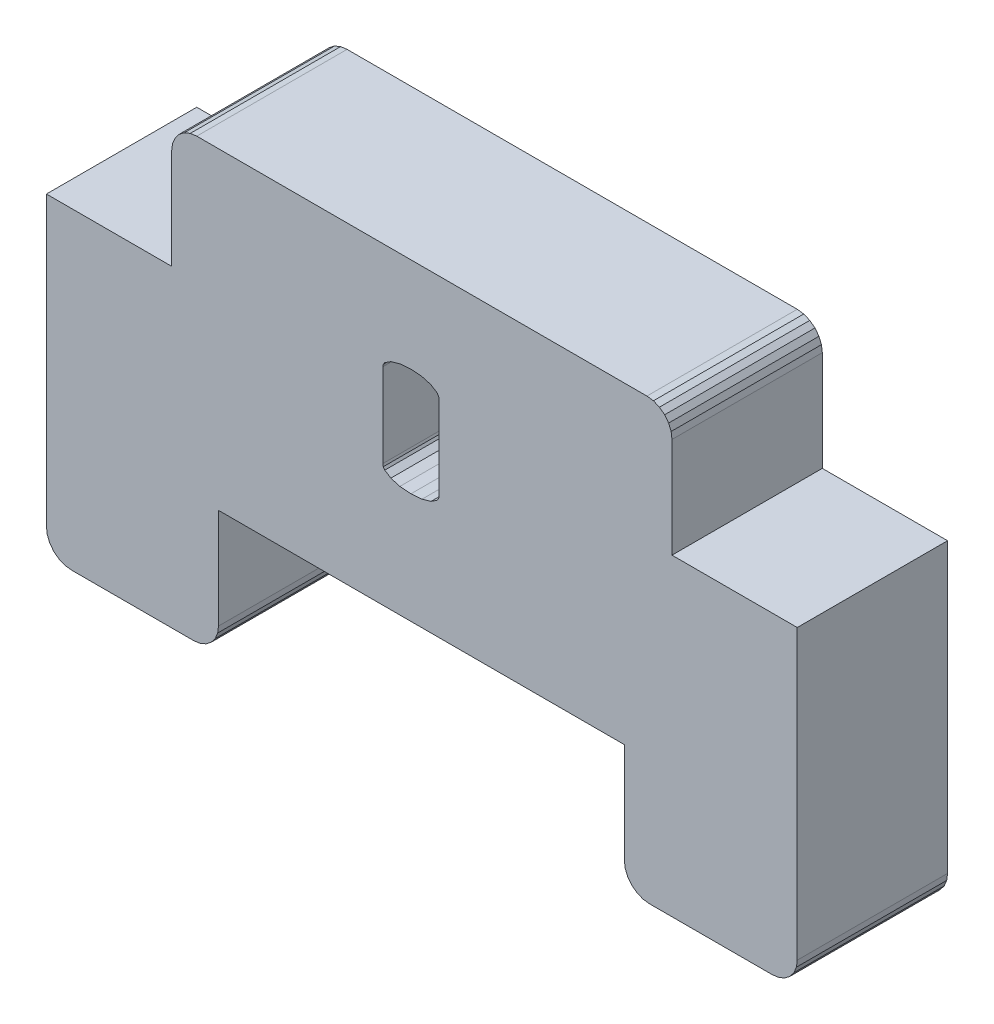
SolidWorks part; units mm, degrees
material "Maple"
ref_plane "Front Plane" through (0, 0, 0) normal (0, 0, 1) x (1, 0, 0)
ref_plane "Top Plane" through (0, 0, 0) normal (0, 1, 0) x (1, 0, 0)
ref_plane "Right Plane" through (0, 0, 0) normal (1, 0, 0) x (0, 0, -1)
sketch "Sketch1" plane through (0, 0, 0) normal (0, 0, 1) x (1, 0, 0)
  line L319 (-339.6271, -185.5951) -> (-339.5272, -185.8363)
  line L320 (-339.6612, -185.3363) -> (-339.6271, -185.5951)
  line L321 (-332.7612, -185.3363) -> (-332.7612, -173.8363)
  line L322 (-333.0541, -186.0434) -> (-333.2612, -186.2023)
  line L323 (-338.2612, -168.9703) -> (-338.5024, -168.8704)
  line L324 (-338.0541, -169.1292) -> (-338.2612, -168.9703)
  line L325 (-337.8952, -169.3363) -> (-338.0541, -169.1292)
  line L326 (-338.6612, -186.3363) -> (-333.7612, -186.3363)
  line L327 (-339.6612, -181.3363) -> (-339.6612, -185.3363)
  line L328 (-355.8612, -181.3363) -> (-339.6612, -181.3363)
  line L329 (-357.7297, -173.8363) -> (-357.7297, -169.8363)
  line L330 (-362.4368, -186.0434) -> (-362.5957, -185.8363)
  line L331 (-362.2297, -186.2023) -> (-362.4368, -186.0434)
  line L332 (-361.9885, -186.3022) -> (-362.2297, -186.2023)
  line L333 (-361.7297, -186.3363) -> (-356.8612, -186.3363)
  line L334 (-337.7612, -173.8363) -> (-332.7612, -173.8363)
  line L335 (-357.4368, -169.1292) -> (-357.2297, -168.9703)
  line L336 (-338.92, -186.3022) -> (-338.6612, -186.3363)
  line L337 (-361.7297, -186.3363) -> (-361.9885, -186.3022)
  line L338 (-356.6024, -186.3022) -> (-356.8612, -186.3363)
  line L339 (-356.9885, -168.8704) -> (-356.7297, -168.8363)
  line L340 (-356.7297, -168.8363) -> (-338.7612, -168.8363)
  line L341 (-333.2612, -186.2023) -> (-333.5024, -186.3022)
  line L342 (-362.7297, -173.8363) -> (-362.7297, -185.3363)
  line L343 (-357.7297, -173.8363) -> (-362.7297, -173.8363)
  line L344 (-357.2297, -168.9703) -> (-356.9885, -168.8704)
  line L345 (-357.5957, -169.3363) -> (-357.4368, -169.1292)
  line L346 (-357.6956, -169.5775) -> (-357.5957, -169.3363)
  line L347 (-357.7297, -169.8363) -> (-357.6956, -169.5775)
  line L348 (-362.6956, -185.5951) -> (-362.7297, -185.3363)
  line L349 (-362.5957, -185.8363) -> (-362.6956, -185.5951)
  line L350 (-356.3612, -186.2023) -> (-356.6024, -186.3022)
  line L351 (-356.1541, -186.0434) -> (-356.3612, -186.2023)
  line L352 (-355.9952, -185.8363) -> (-356.1541, -186.0434)
  line L353 (-355.8953, -185.5951) -> (-355.9952, -185.8363)
  line L354 (-355.8612, -185.3363) -> (-355.8953, -185.5951)
  line L355 (-355.8612, -185.3363) -> (-355.8612, -181.3363)
  line L356 (-339.5272, -185.8363) -> (-339.3683, -186.0434)
  line L357 (-339.3683, -186.0434) -> (-339.1612, -186.2023)
  line L358 (-339.1612, -186.2023) -> (-338.92, -186.3022)
  line L359 (-333.5024, -186.3022) -> (-333.7612, -186.3363)
  line L360 (-332.8952, -185.8363) -> (-333.0541, -186.0434)
  line L361 (-332.7953, -185.5951) -> (-332.8952, -185.8363)
  line L362 (-332.7612, -185.3363) -> (-332.7953, -185.5951)
  line L363 (-337.7612, -169.8363) -> (-337.7612, -173.8363)
  line L364 (-337.7612, -169.8363) -> (-337.7953, -169.5775)
  line L365 (-337.7953, -169.5775) -> (-337.8952, -169.3363)
  line L366 (-338.5024, -168.8704) -> (-338.7612, -168.8363)
  line L8572 (-349.3045, -176.444) -> (-349.2844, -176.5403)
  line L8573 (-349.2844, -176.5403) -> (-349.2241, -176.629)
  line L8574 (-349.2241, -176.629) -> (-348.9829, -176.7844)
  line L8575 (-348.9829, -176.7844) -> (-348.6216, -176.8897)
  line L8576 (-348.6216, -176.8897) -> (-348.1806, -176.9249)
  line L8577 (-348.1806, -176.9249) -> (-347.7396, -176.8897)
  line L8578 (-347.7396, -176.8897) -> (-347.3782, -176.7844)
  line L8579 (-347.3782, -176.7844) -> (-347.1371, -176.629)
  line L8580 (-347.1371, -176.629) -> (-347.0768, -176.5403)
  line L8581 (-347.0768, -176.5403) -> (-347.0567, -176.444)
  line L8582 (-347.0567, -176.444) -> (-347.0567, -173.0973)
  line L8583 (-347.0567, -173.0973) -> (-347.0768, -173.0012)
  line L8584 (-347.0768, -173.0012) -> (-347.1371, -172.9124)
  line L8585 (-347.1371, -172.9124) -> (-347.3782, -172.757)
  line L8586 (-347.3782, -172.757) -> (-347.7396, -172.6517)
  line L8587 (-347.7396, -172.6517) -> (-348.1806, -172.6165)
  line L8588 (-348.1806, -172.6165) -> (-348.6216, -172.6517)
  line L8589 (-348.6216, -172.6517) -> (-348.9829, -172.757)
  line L8590 (-348.9829, -172.757) -> (-349.2241, -172.9124)
  line L8591 (-349.2241, -172.9124) -> (-349.2844, -173.0012)
  line L8592 (-349.2844, -173.0012) -> (-349.3045, -173.0973)
  line L8593 (-349.3045, -173.0973) -> (-349.3045, -176.444)
  line L8594 (-347.0567, -176.444) -> (-347.0768, -176.5403)
  line L8595 (-347.0768, -176.5403) -> (-347.1371, -176.629)
  line L8596 (-347.1371, -176.629) -> (-347.3782, -176.7844)
  line L8597 (-347.3782, -176.7844) -> (-347.7396, -176.8897)
  line L8598 (-347.7396, -176.8897) -> (-348.1806, -176.9249)
  line L8599 (-348.1806, -176.9249) -> (-348.6216, -176.8897)
  line L8600 (-348.6216, -176.8897) -> (-348.9829, -176.7844)
  line L8601 (-348.9829, -176.7844) -> (-349.2241, -176.629)
  line L8602 (-349.2241, -176.629) -> (-349.2844, -176.5403)
  line L8603 (-349.2844, -176.5403) -> (-349.3045, -176.444)
  line L8604 (-349.3045, -176.444) -> (-349.3045, -173.0973)
  line L8605 (-349.3045, -173.0973) -> (-349.2844, -173.0012)
  line L8606 (-349.2844, -173.0012) -> (-349.2241, -172.9124)
  line L8607 (-349.2241, -172.9124) -> (-348.9829, -172.757)
  line L8608 (-348.9829, -172.757) -> (-348.6216, -172.6517)
  line L8609 (-348.6216, -172.6517) -> (-348.1806, -172.6165)
  line L8610 (-348.1806, -172.6165) -> (-347.7396, -172.6517)
  line L8611 (-347.7396, -172.6517) -> (-347.3782, -172.757)
  line L8612 (-347.3782, -172.757) -> (-347.1371, -172.9124)
  line L8613 (-347.1371, -172.9124) -> (-347.0768, -173.0012)
  line L8614 (-347.0768, -173.0012) -> (-347.0567, -173.0973)
  line L8615 (-347.0567, -173.0973) -> (-347.0567, -176.444)
  line L8616 (-348.0245, -176.3196) -> (-347.0629, -177.5373)
extrude "Boss-Extrude1" add sketch "Sketch1" along normal blind 6 contours L323 L366 L340 L339 L344 L335 L345 L346 L347 L329 L343 L342 L348 L349 L330 L331 L332 L337 L333 L338 L350 L351 L352 L353 L354 L355 L328 L327 L320 L319 L356 L357 L358 L336 L326 L359 L341 L322 L360 L361 L362 L321 L334 L363 L364 L365 L325 L324 L8593 L8592
